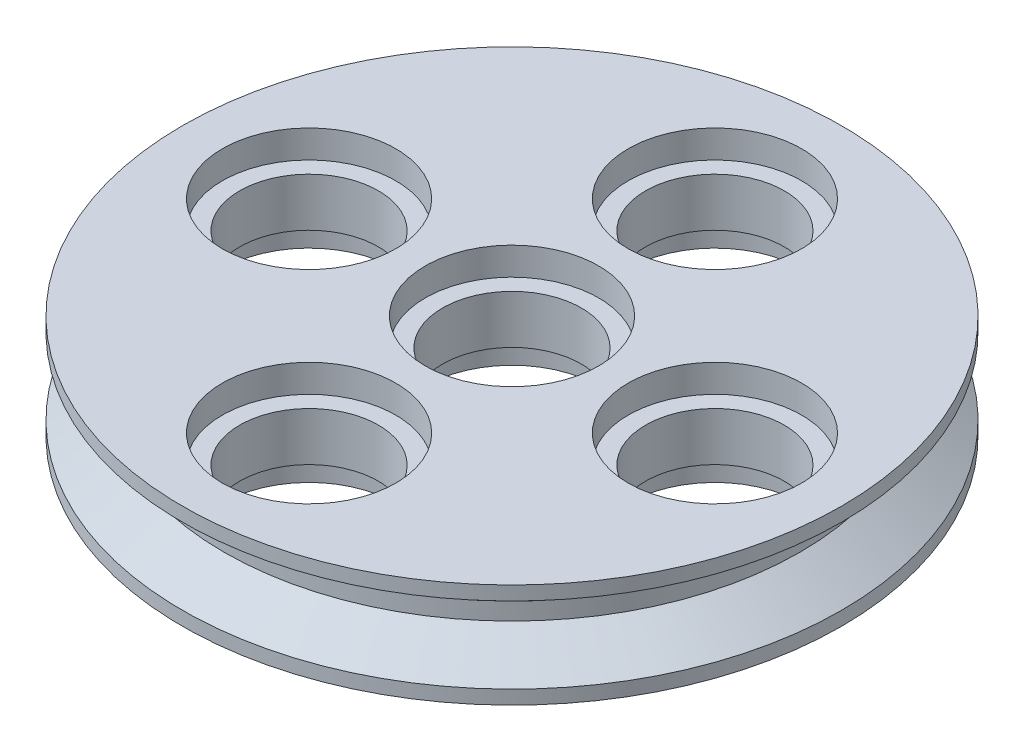
SolidWorks part; units mm, degrees
material "ABS"
ref_plane "Front Plane" through (0, 0, 0) normal (0, 0, 1) x (1, 0, 0)
ref_plane "Top Plane" through (0, 0, 0) normal (0, 1, 0) x (1, 0, 0)
ref_plane "Right Plane" through (0, 0, 0) normal (1, 0, 0) x (0, 0, -1)
sketch "Sketch2" plane through (0, 0, 0) normal (0, 0, 1) x (1, 0, 0)
  line L0 (9.5, 0.75) -> (9.5, 0.35)
  line L1 (0, 0.75) -> (9.5, 0.75)
  line L2 (0, 0.75) -> (0, -0.75)
  line L5 (9.5, 0.35) -> (8.3007, -0.5)
  line L6 (8.3007, -0.5) -> (8.3007, -0.75)
  line L7 (0, -0.75) -> (8.3007, -0.75)
  dimension "D1" = 9.5
  dimension "D2" = 1.5
  dimension "D3" = 0.4
  dimension "D4" = 0.25
  dimension "D5" = 1.47
revolve "Revolve1" add sketch "Sketch2" angle 360 about L2
hole_wizard "Hole1" positions "Sketch5" profile "Sketch6" legacy end condition through all
sketch "Sketch5" plane through (0, 0.75, 0) normal (0, 1, 0) x (1, 0, 0)
  circle A0 centre (0, 0) radius 9.5 construction
  point P0 (0, 0)
  point P3 (-5.85, 0)
  point P5 (5.85, 0)
  point P7 (0, 5.85)
  point P9 (0, -5.85)
  dimension "D1" = 5.85
  dimension "D2" = 5.85
  dimension "D3" = 5.85
  dimension "D4" = 5.85
sketch "Sketch6" plane through (0, 0.75, 0) normal (1, 0, 0) x (0, 0, 1)
  line L0 (0, 0) -> (0, 2.7017)
  line L1 (0, 2.7017) -> (2, 1.5)
  line L2 (2, 1.5) -> (2, 0.8)
  line L3 (2, 0.8) -> (2.5, 0.8)
  line L4 (2.5, 0) -> (0, 0)
  line L5 (0, -11.3109) -> (0, 121.1557) construction
  line L6 (0, 2.7017) -> (-2, 1.5) construction
  line L7 (2.5, 0.8) -> (2.5, 0)
  dimension "Depth" = 1.5
  dimension "Drill Angle" = 118
  dimension "Diameter" = 4
  dimension "C-Bore Diameter" = 5
  dimension "C-Bore Depth" = 0.8
mirror "Mirror1" about plane through (0, -0.75, 0) normal (0, 1, 0) of bodies 102
